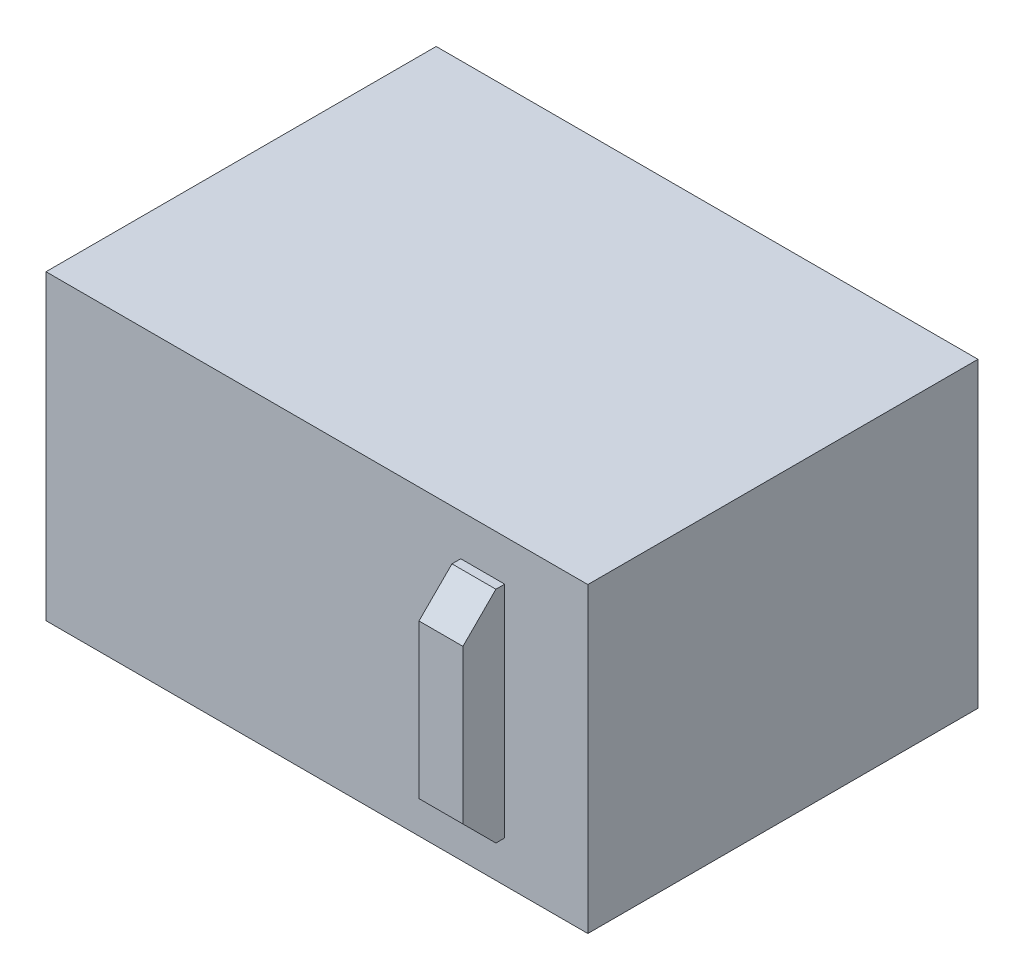
SolidWorks part; units mm, degrees
ref_plane "Front Plane" through (0, 0, 0) normal (0, 0, 1) x (1, 0, 0)
ref_plane "Top Plane" through (0, 0, 0) normal (0, 1, 0) x (1, 0, 0)
ref_plane "Right Plane" through (0, 0, 0) normal (1, 0, 0) x (0, 0, -1)
sketch "Sketch1" plane through (0, 0, 0) normal (0, 1, 0) x (1, 0, 0)
  line L1 (246.5, -177.5) -> (-246.5, -177.5)
  line L2 (246.5, -177.5) -> (246.5, 177.5)
  line L3 (246.5, 177.5) -> (-246.5, 177.5)
  line L4 (-246.5, -177.5) -> (-246.5, 177.5)
  line L5 (246.5, -177.5) -> (-246.5, 177.5) construction
  line L6 (246.5, 177.5) -> (-246.5, -177.5) construction
  point P0 (0, 0)
  dimension "D1" = 355
  dimension "D2" = 493
extrude "Boss-Extrude1" add sketch "Sketch1" along normal blind 275
sketch "Sketch2" plane through (0, 0, 177.5) normal (0, 0, 1) x (1, 0, 0)
  line L0 (246.5, 275) -> (246.5, 0) construction
  line L1 (170.8685, 37.5) -> (130.8685, 37.5)
  line L2 (170.8685, 37.5) -> (170.8685, 237.5)
  line L3 (170.8685, 237.5) -> (130.8685, 237.5)
  line L4 (130.8685, 37.5) -> (130.8685, 237.5)
  line L5 (170.8685, 37.5) -> (130.8685, 237.5) construction
  line L6 (170.8685, 237.5) -> (130.8685, 37.5) construction
  point P0 (150.8685, 137.5)
  point P9 (246.5, 137.5)
  dimension "D1" = 200
  dimension "D2" = 40
extrude "Boss-Extrude2" add sketch "Sketch2" along normal blind 38
chamfer "Chamfer1" distance 30 angle 45 2 edges at (150.8685, 37.5, 215.5) (150.8685, 237.5, 215.5)
